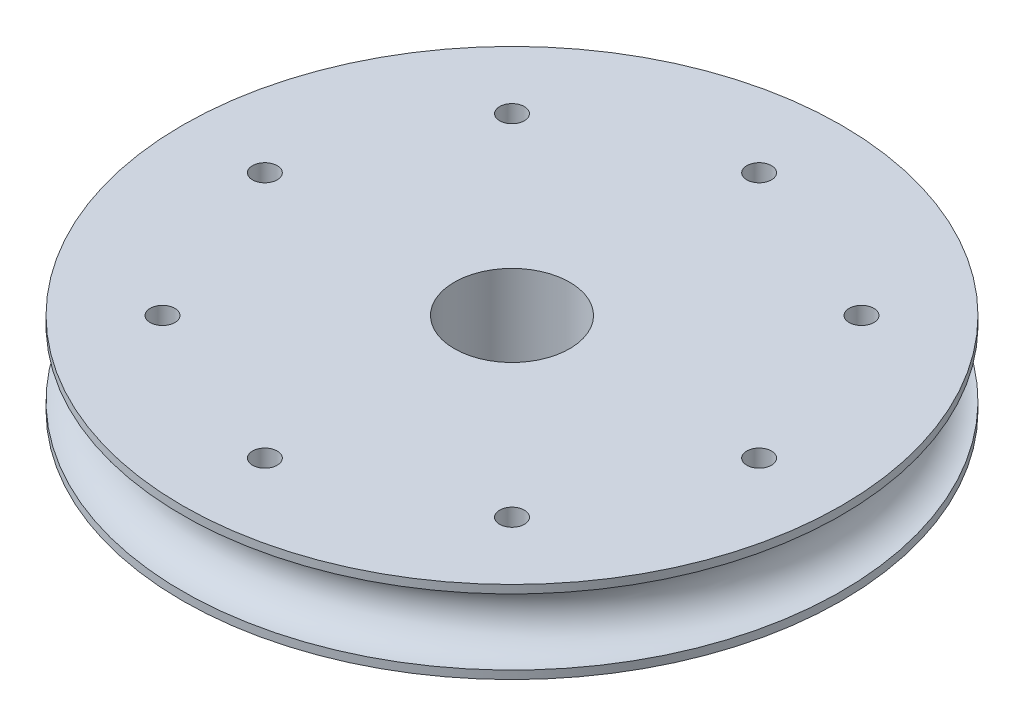
SolidWorks part; units mm, degrees
ref_plane "Front Plane" through (0, 0, 0) normal (0, 0, 1) x (1, 0, 0)
ref_plane "Top Plane" through (0, 0, 0) normal (0, 1, 0) x (1, 0, 0)
ref_plane "Right Plane" through (0, 0, 0) normal (1, 0, 0) x (0, 0, -1)
sketch "Sketch1" plane through (0, 0, 0) normal (0, 1, 0) x (1, 0, 0)
  circle A0 centre (0, 0) radius 20
  circle A1 centre (0, 0) radius 3.5
  dimension "D1" = 40
  dimension "D2" = 7
extrude "Boss-Extrude1" add sketch "Sketch1" along normal blind 5
sketch "Sketch2" plane through (0, 0, 0) normal (0, 0, 1) x (1, 0, 0)
  line L0 (-20, 0.5) -> (-20, 4.5)
  line L1 (-20, 5) -> (-20, 0) construction
  line L2 (-20, 0) -> (-20, 5) construction
  line L3 (0, 0) -> (0, 5) construction
  line L4 (3.5, 5) -> (-3.5, 5) construction
  arc A0 (-20, 0.5) -> (-20, 4.5) centre (-20, 2.5) ccw
  dimension "D1" = 2
revolve "Cut-Revolve1" cut sketch "Sketch2" angle 360 about L3
sketch "Sketch3" plane through (0, 0, 0) normal (0, 1, 0) x (1, 0, 0)
  circle A0 centre (0, -15) radius 0.75
  circle A1 centre (-10.6066, -10.6066) radius 0.75
  circle A2 centre (-15, 0) radius 0.75
  circle A3 centre (-10.6066, 10.6066) radius 0.75
  circle A4 centre (0, 15) radius 0.75
  circle A5 centre (10.6066, 10.6066) radius 0.75
  circle A6 centre (15, 0) radius 0.75
  circle A7 centre (10.6066, -10.6066) radius 0.75
  point P2 (0, 0)
  point P4 (0, 0)
  point P20 (0, 0)
  dimension "D1" = 15
  dimension "D3" = 1.5
  dimension "D2" = 8
extrude "Cut-Extrude1" cut sketch "Sketch3" along normal through all
